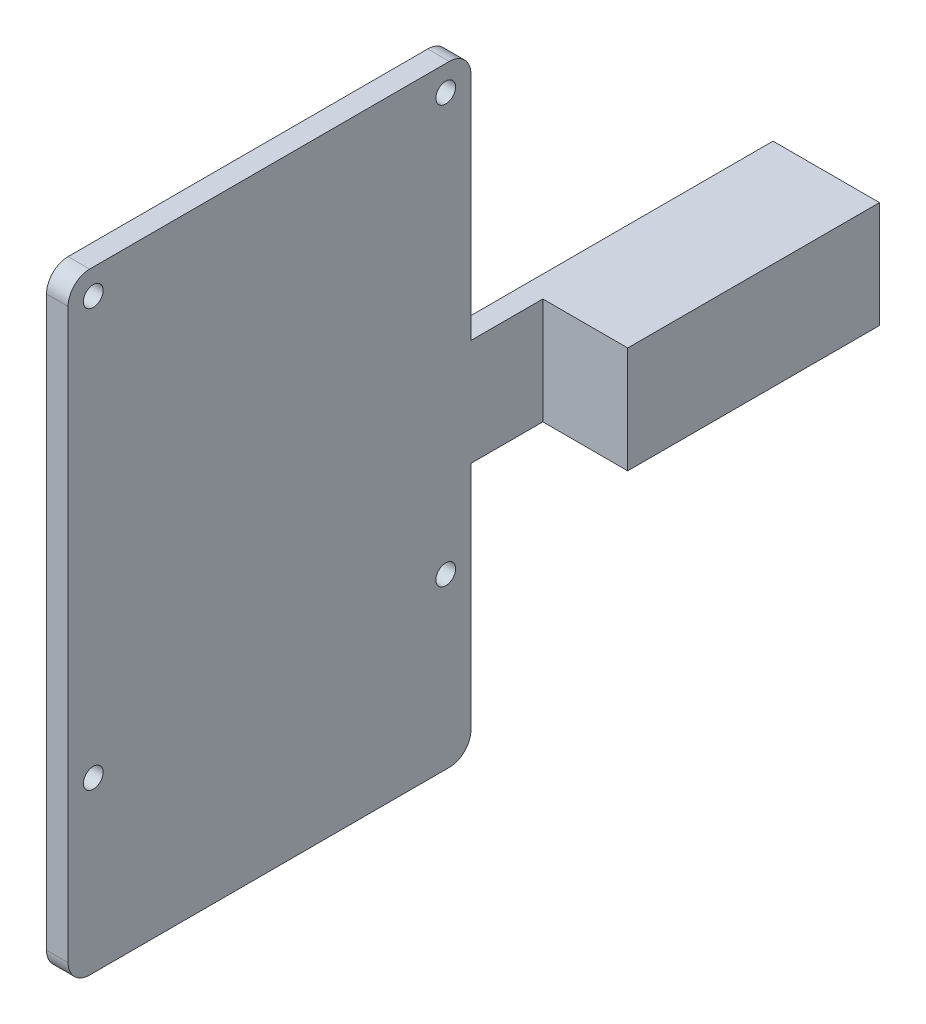
SolidWorks part; units mm, degrees
ref_plane "Front Plane" through (0, 0, 0) normal (0, 0, 1) x (1, 0, 0)
ref_plane "Top Plane" through (0, 0, 0) normal (0, 1, 0) x (1, 0, 0)
ref_plane "Right Plane" through (0, 0, 0) normal (1, 0, 0) x (0, 0, -1)
sketch "Sketch1" plane through (0, 0, 0) normal (0, 0, 1) x (1, 0, 0)
  line L1 (7.4, -7.4) -> (-7.4, -7.4)
  line L2 (7.4, -7.4) -> (7.4, 7.4)
  line L3 (7.4, 7.4) -> (-7.4, 7.4)
  line L4 (-7.4, -7.4) -> (-7.4, 7.4)
  line L5 (7.4, -7.4) -> (-7.4, 7.4) construction
  line L6 (7.4, 7.4) -> (-7.4, -7.4) construction
  point P0 (0, 0)
  dimension "D1" = 14.8
  dimension "D2" = 14.8
extrude "Boss-Extrude1" add sketch "Sketch1" along normal blind 35
sketch "Sketch3" plane through (0, 0, 35) normal (0, 0, 1) x (1, 0, 0)
  line L0 (-7.4, -7.4) -> (7.4, -7.4) construction
  line L1 (-7.4, 7.4) -> (-4.4, 7.4)
  line L2 (-7.4, 7.4) -> (-7.4, -7.4)
  line L3 (-7.4, -7.4) -> (-4.4, -7.4)
  line L4 (-4.4, 7.4) -> (-4.4, -7.4)
  dimension "D1" = 3
extrude "Boss-Extrude3" add sketch "Sketch3" along normal blind 10
sketch "Sketch5" plane through (0, 0, 45) normal (0, 0, 1) x (1, 0, 0)
  line L0 (-4.4, -7.4) -> (-4.4, 7.4) construction
  line L1 (-7.4, -42.5) -> (-4.4, -42.5)
  line L2 (-7.4, -42.5) -> (-7.4, 42.5)
  line L3 (-7.4, 42.5) -> (-4.4, 42.5)
  line L4 (-4.4, -42.5) -> (-4.4, 42.5)
  line L5 (-7.4, 7.4) -> (-7.4, -7.4) construction
  line L6 (-4.4, 0) -> (-7.4, 0) construction
  line L7 (-4.4, 0) -> (-7.4, 0) construction
  dimension "D1" = 85
extrude "Boss-Extrude4" add sketch "Sketch5" along normal blind 56
sketch "Sketch6" plane through (-4.4, 0, 0) normal (1, 0, 0) x (0, 0, -1)
  line L0 (-101, -42.5) -> (-101, 42.5) construction
  line L1 (-101, 42.5) -> (-45, 42.5) construction
  circle A0 centre (-97.5, 39) radius 1.375
  circle A1 centre (-48.5, 39) radius 1.375
  circle A2 centre (-48.5, -19) radius 1.375
  circle A3 centre (-97.5, -19) radius 1.375
  dimension "D1" = 2.75
  dimension "D2" = 2.75
  dimension "D3" = 2.75
  dimension "D4" = 2.75
  dimension "D5" = 49
  dimension "D6" = 58
  dimension "D7" = 3.5
  dimension "D8" = 3.5
extrude "Cut-Extrude1" cut sketch "Sketch6" against normal blind 5
fillet "Fillet2" radius 3 4 edges at (-5.9, -42.5, 45) (-5.9, -42.5, 101) (-5.9, 42.5, 45) (-5.9, 42.5, 101)
